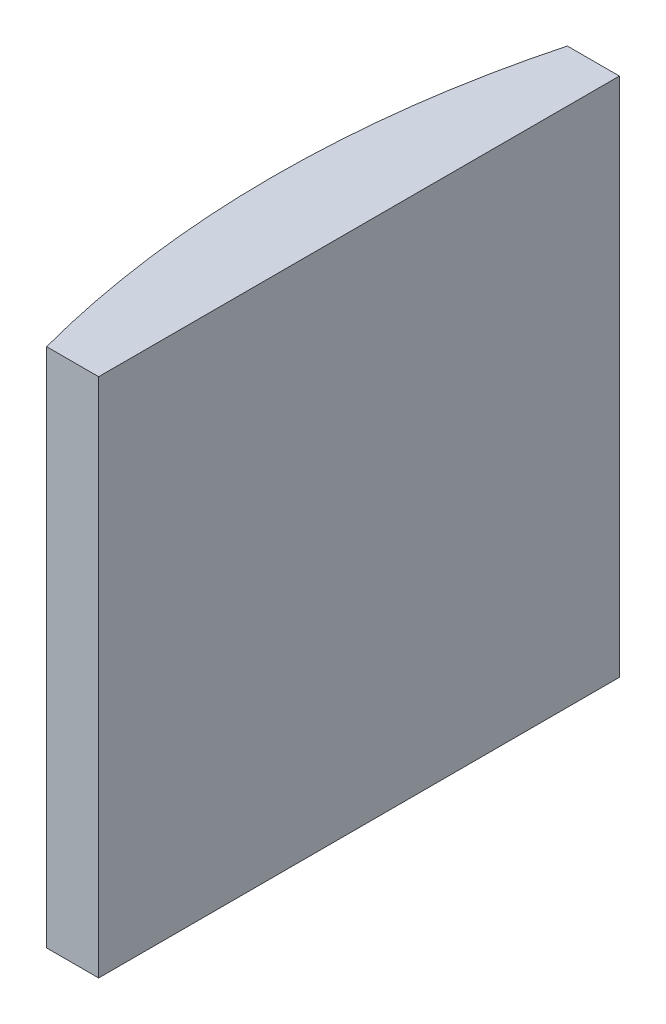
SolidWorks part; units mm, degrees
ref_plane "前视基准面" through (0, 0, 0) normal (0, 0, 1) x (1, 0, 0)
ref_plane "上视基准面" through (0, 0, 0) normal (0, 1, 0) x (1, 0, 0)
ref_plane "右视基准面" through (0, 0, 0) normal (1, 0, 0) x (0, 0, -1)
sketch "草图1" plane through (0, 0, 0) normal (0, 1, 0) x (1, 0, 0)
  line L0 (10.7432, 0) -> (-46.484, 0) construction
  line L1 (-33.1133, 10) -> (-31.1148, 10)
  line L2 (-33.1133, -10) -> (-31.1148, -10)
  line L3 (-31.1148, 10) -> (-31.1148, -10)
  arc A0 (-33.1133, 10) -> (-33.1133, -10) centre (4.3552, 0) ccw
  point P2 (-46.484, 0)
  point P19 (-34.4248, 0)
  point P20 (-31.1148, 0)
  dimension "D2" = 10
  dimension "D3" = 38.78
  dimension "D4" = 3.31
  dimension "D1" = 10
extrude "凸台-拉伸1" add sketch "草图1" along normal blind 20
